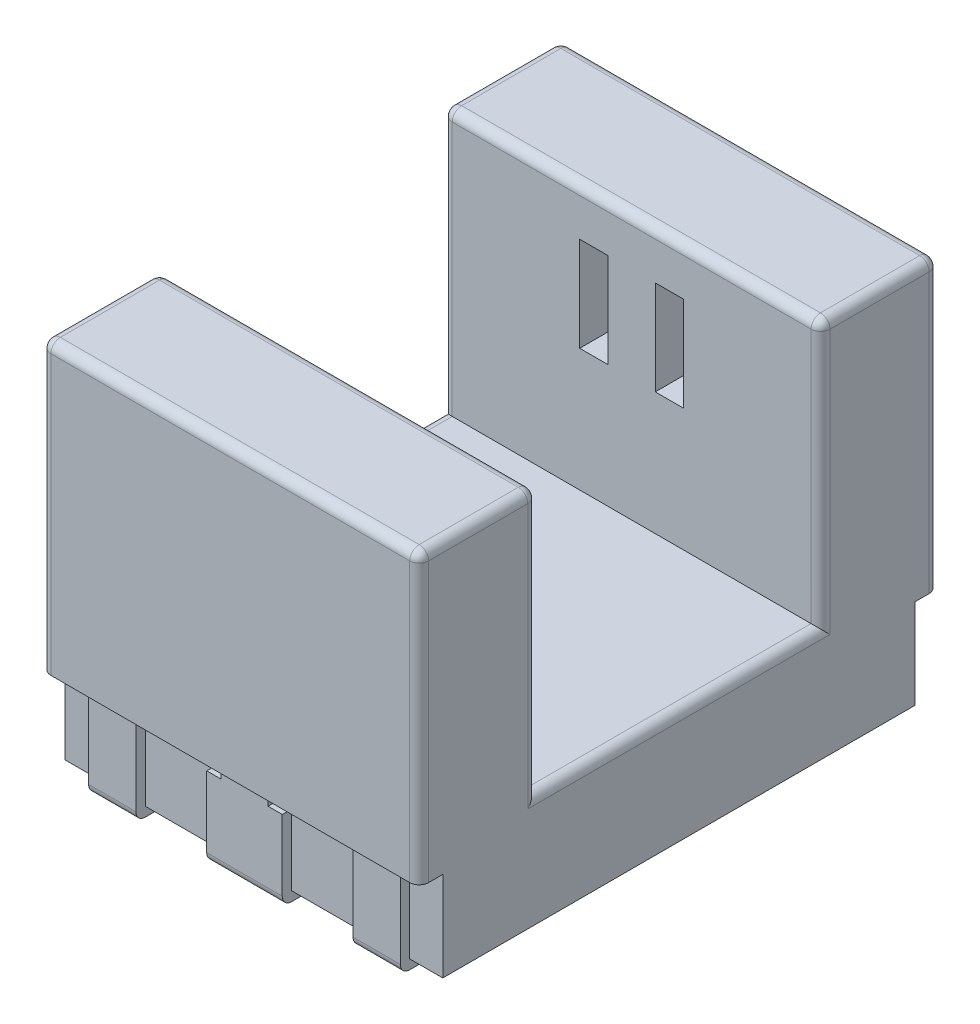
SolidWorks part; units mm, degrees
ref_plane "Plan de face" through (0, 0, 0) normal (0, 0, 1) x (1, 0, 0)
ref_plane "Plan de dessus" through (0, 0, 0) normal (0, 1, 0) x (1, 0, 0)
ref_plane "Plan de droite" through (0, 0, 0) normal (1, 0, 0) x (0, 0, -1)
sketch "Esquisse1" plane through (0, 0, 0) normal (0, 1, 0) x (1, 0, 0)
  line L0 (-2, 2.5) -> (2, -2.5) construction
  line L1 (-2, -2.5) -> (2, -2.5)
  line L2 (-2, -2.5) -> (-2, 2.5)
  line L3 (-2, 2.5) -> (2, 2.5)
  line L4 (2, -2.5) -> (2, 2.5)
  point P4 (0, 0)
  dimension "D1" = 4
  dimension "D2" = 5
extrude "Boss.-Extru.1" add sketch "Esquisse1" along normal blind 4
sketch "Esquisse3" plane through (2, 0, 0) normal (1, 0, 0) x (0, 0, -1)
  line L0 (-2.5, 4) -> (2.5, 4) construction
  line L1 (-1.5, 4) -> (1.5, 4)
  line L2 (-1.5, 4) -> (-1.5, 1.2)
  line L3 (-1.5, 1.2) -> (1.5, 1.2)
  line L4 (1.5, 4) -> (1.5, 1.2)
  line L5 (-2.5, 4) -> (-2.5, 0) construction
  dimension "D1" = 3
  dimension "D2" = 2.8
  dimension "D3" = 1
extrude "Enlèv. mat.-Extru.1" cut sketch "Esquisse3" against normal blind 4
sketch "Esquisse4" plane through (0, 0, 2.5) normal (0, 0, 1) x (1, 0, 0)
  line L0 (2, 4) -> (2, 0) construction
  line L1 (-2, 4) -> (2, 4)
  line L2 (-2, 4) -> (-2, 0.95)
  line L3 (-2, 0.95) -> (2, 0.95)
  line L4 (2, 4) -> (2, 0.95)
  line L5 (-2, 0) -> (2, 0) construction
  dimension "D1" = 0.95
extrude "Boss.-Extru.2" add sketch "Esquisse4" along normal blind 0.25
mirror "Symétrie1" about plane through (0, 0, 0) normal (0, 0, 1) of "Boss.-Extru.2"
sketch "Esquisse5" plane through (0, 0, 2.5) normal (0, 0, 1) x (1, 0, 0)
  line L0 (-2, 0) -> (2, 0) construction
  line L1 (-0.25, 0) -> (0.25, 0)
  line L2 (-0.25, 0) -> (-0.25, 0.95)
  line L3 (-0.25, 0.95) -> (0.25, 0.95)
  line L4 (0.25, 0) -> (0.25, 0.95)
  line L5 (-2, 0.95) -> (2, 0.95) construction
  line L6 (1.15, 0) -> (1.15, 0.95)
  line L7 (1.15, 0) -> (1.65, 0)
  line L8 (1.65, 0) -> (1.65, 0.95)
  line L9 (1.15, 0.95) -> (1.65, 0.95)
  line L10 (-0.25, 0) -> (-0.25, 0.95)
  line L11 (-0.25, 0) -> (0.25, 0)
  line L12 (0.25, 0) -> (0.25, 0.95)
  line L13 (-0.25, 0.95) -> (0.25, 0.95)
  line L14 (-1.65, 0) -> (-1.65, 0.95)
  line L15 (-1.65, 0) -> (-1.15, 0)
  line L16 (-1.15, 0) -> (-1.15, 0.95)
  line L17 (-1.65, 0.95) -> (-1.15, 0.95)
  line L18 (-0.25, 0) -> (1.15, 0) construction
  point P8 (0, 0)
  line M17 (2, 0.95) -> (-2, 0.95)
  line M19 (-2, 0) -> (2, 0)
  dimension "D1" = 0.5
  dimension "D4" = 1.4
  dimension "D5" = 0.95
  dimension "D6" = 1.4
  dimension "D2" = 2
  dimension "D3" = 2
extrude "Boss.-Extru.3" add sketch "Esquisse5" along normal blind 0.1 contours L16 L14 M19 M17 | L4 L2 M19 M17 | L8 L6 M19 M17
sketch "Esquisse6" plane through (0, 0, 0) normal (0, -1, 0) x (1, 0, 0)
  line L0 (-0.25, 2.6) -> (-0.25, 1.58)
  line L1 (-1.65, 2.6) -> (-1.15, 2.6)
  line L2 (-1.65, 2.6) -> (-1.65, 1.58)
  line L3 (-1.65, 1.58) -> (-1.15, 1.58)
  line L4 (-1.15, 2.6) -> (-1.15, 1.58)
  line L5 (-0.25, 2.6) -> (0.25, 2.6)
  line L6 (0.25, 2.6) -> (0.25, 1.58)
  line L7 (-0.25, 1.58) -> (0.25, 1.58)
  line L8 (1.15, 2.6) -> (1.15, 1.58)
  line L9 (1.15, 2.6) -> (1.65, 2.6)
  line L10 (1.65, 2.6) -> (1.65, 1.58)
  line L11 (1.15, 1.58) -> (1.65, 1.58)
  line L12 (-1.65, 2.6) -> (-0.25, 2.6) construction
  dimension "D1" = 0.5
  dimension "D2" = 1.02
  dimension "D4" = 1.4
  dimension "D3" = 3
extrude "Boss.-Extru.4" add sketch "Esquisse6" along normal blind 0.1
mirror "Symétrie2" about plane through (0, 0, 0) normal (0, 0, 1) of "Boss.-Extru.3", "Boss.-Extru.4"
sketch "Esquisse7" plane through (0, -0.1, 0) normal (0, -1, 0) x (1, 0, 0)
  line L0 (0.25, 2.6) -> (-0.25, 2.6) construction
  line L1 (-0.4, 1.58) -> (0.4, 1.58)
  line L2 (-0.4, 1.58) -> (-0.4, 2.6)
  line L3 (-0.4, 2.6) -> (0.4, 2.6)
  line L4 (0.4, 1.58) -> (0.4, 2.6)
  line L5 (0.25, 1.58) -> (0.25, 2.6) construction
  line L6 (-0.4, 2.6) -> (0.4, 1.58) construction
  line L7 (-0.25, 2.6) -> (-0.25, 1.58) construction
  line L8 (-0.25, 1.58) -> (0.25, 1.58) construction
  dimension "D1" = 0.8
  dimension "D2" = 0.15
extrude "Boss.-Extru.5" add sketch "Esquisse7" against normal up to surface (0.1 mm away) up to face at (0, 0, 0)
sketch "Esquisse8" plane through (0, 0, 2.6) normal (0, 0, 1) x (1, 0, 0)
  line L0 (0.4, 0) -> (0.4, -0.1) construction
  line L1 (-0.4, 0) -> (0.4, 0)
  line L2 (-0.4, 0) -> (-0.4, 0.75)
  line L3 (-0.4, 0.75) -> (0.4, 0.75)
  line L4 (0.4, 0) -> (0.4, 0.75)
  line L5 (-2, 0.95) -> (2, 0.95) construction
  dimension "D1" = 0.2
extrude "Boss.-Extru.6" add sketch "Esquisse8" against normal up to surface (0.1 mm away) up to face at (0.64, 0.38, 2.5)
sketch "Esquisse9" plane through (0, 0, 1.5) normal (0, 0, -1) x (-1, 0, 0)
  line L0 (2, 4) -> (-2, 4) construction
  line L1 (-1.25, 3.5) -> (1.25, 3.5)
  line L2 (-1.25, 3.5) -> (-1.25, 2)
  line L3 (-1.25, 2) -> (1.25, 2)
  line L4 (1.25, 3.5) -> (1.25, 2)
  line L5 (0, 4) -> (0, 1.2) construction
  line L6 (2, 1.2) -> (-2, 1.2) construction
  point P12 (0, 3.5)
  dimension "D1" = 1.5
  dimension "D2" = 2.5
  dimension "D3" = 0.5
extrude "Enlèv. mat.-Extru.2" cut sketch "Esquisse9" against normal blind 0.7 contours L2 L1 L4 L3
sketch "Esquisse10" plane through (0, 0, -1.5) normal (0, 0, 1) x (1, 0, 0)
  line L0 (0.25, 3.5) -> (0.55, 2.5) construction
  line L1 (0.25, 3.5) -> (0.55, 3.5)
  line L2 (0.25, 3.5) -> (0.25, 2.5)
  line L3 (0.25, 2.5) -> (0.55, 2.5)
  line L4 (0.55, 3.5) -> (0.55, 2.5)
  line L5 (-2, 4) -> (2, 4) construction
  line L6 (0, 4) -> (0, 1.2) construction
  line L7 (-2, 1.2) -> (2, 1.2) construction
  line L8 (-0.25, 2.5) -> (-0.55, 2.5)
  line L9 (-0.55, 3.5) -> (-0.55, 2.5)
  line L10 (-0.25, 3.5) -> (-0.55, 3.5)
  line L11 (-0.25, 3.5) -> (-0.25, 2.5)
  point P4 (0.4, 3)
  dimension "D1" = 0.3
  dimension "D2" = 1
  dimension "D3" = 0.4
  dimension "D4" = 1
extrude "Enlèv. mat.-Extru.3" cut sketch "Esquisse10" against normal blind 0.3
sketch "Esquisse11" plane through (0, 0, 0) normal (0, -1, 0) x (1, 0, 0)
  line L0 (0.5, -0.6) -> (0.9, -1)
  line L1 (0.2, 0) -> (-0.2, 0)
  line L2 (0.2, 1) -> (0.2, -1)
  line L3 (0.2, -1) -> (-0.2, -1)
  line L4 (-0.2, 1) -> (-0.2, -1)
  line L5 (0.9, -1) -> (0.5, -1)
  line L6 (0.5, -1) -> (0.5, -0.6)
  line L7 (2, 2.5) -> (-2, -2.5) construction
  line L8 (2, 0) -> (-2, 0) construction
  line L9 (2, 2.5) -> (2, -2.5) construction
  line L10 (-2, -2.5) -> (-2, 2.5) construction
  line L11 (0, 2.5) -> (0, -2.6) construction
  line L12 (0.25, -2.6) -> (-0.25, -2.6) construction
  line L13 (0.9, 1) -> (0.5, 1)
  line L14 (0.5, 0.6) -> (0.9, 1)
  line L15 (0.5, 1) -> (0.5, 0.6)
  line L16 (0.2, 1) -> (-0.2, 1)
  line L17 (-0.9, -1) -> (-0.5, -1)
  line L18 (-0.5, -0.6) -> (-0.9, -1)
  line L19 (-0.5, -1) -> (-0.5, -0.6)
  line L20 (-0.2, 1) -> (-0.2, -1)
  line L21 (0.2, 1) -> (0.2, -1)
  line L22 (-0.5, 0.6) -> (-0.9, 1)
  line L23 (-0.5, 1) -> (-0.5, 0.6)
  line L24 (-0.9, 1) -> (-0.5, 1)
  line L25 (1, -0.2) -> (1, 0.2)
  line L26 (1, 0.2) -> (-1, 0.2)
  line L27 (-1, -0.2) -> (-1, 0.2)
  line L28 (1, -0.2) -> (-1, -0.2)
  line L29 (-0.2, -1) -> (0.2, -1)
  line L30 (0.2, -1) -> (0.2, 1)
  line L31 (-0.2, 1) -> (0.2, 1)
  line L32 (-0.2, -1) -> (-0.2, 1)
  line L33 (-1, 0.2) -> (-1, -0.2)
  line L34 (-1, -0.2) -> (1, -0.2)
  line L35 (1, 0.2) -> (1, -0.2)
  line L36 (-1, 0.2) -> (1, 0.2)
  point P11 (0, 0)
  point P49 (0, 0)
  dimension "D1" = 1
  dimension "D2" = 0
  dimension "D3" = 0
  dimension "D4" = 0.4
  dimension "D5" = 0.3
  dimension "D6" = 0.4
  dimension "D7" = 0.4
  dimension "D8" = 4
extrude "Enlèv. mat.-Extru.4" cut sketch "Esquisse11" against normal blind 0.3 contours L17 L19 L18 | L28 L4 L20 L26 L27 | L21 L26 L20 L1 | L21 L28 L20 L3 | L26 L2 L16 L4 | L24 L22 L23 | L13 L15 L14 | L6 L5 L0
fillet "Congé1" radius 0.1 18 edges at (-2, 2.475, 2.75) (2, 1.2, 0) (2, 2.475, 2.75) (2, 2.6, 1.5) (0, 4, 2.75) (2, 4, 2.125) (-2, 4, 2.125) (0, 4, 1.5) (-2, 2.6, 1.5) (-2, 1.2, 0) (-2, 4, -2.125) (-2, 2.6, -1.5) (-2, 2.475, -2.75) (2, 2.475, -2.75) (0, 4, -1.5) (0, 4, -2.75) (2, 2.6, -1.5) (2, 4, -2.125)
fillet "Congé2" radius 0.1 6 edges at (1.4, -0.1, -2.6) (0, -0.1, -2.6) (-1.4, -0.1, -2.6) (1.4, -0.1, 2.6) (0, -0.1, 2.6) (-1.4, -0.1, 2.6)
fillet "Congé3" radius 0.05 70 edges at (0.7, 0, -0.8) (-0.2, 0, 0.6) (-0.5, 0.15, -0.6) (-0.7, 0.3, -0.8) (-0.7, 0, -0.8) (-0.9, 0.15, -1) (-0.7, 0.3, -1) (-0.5, 0.15, -1) (-0.7, 0, -1) (0.6, 0, 0.2) (1, 0.15, 0.2) (0.2, 0.15, 0.2) (1, 0.15, -0.2) (0.6, 0, -0.2) (0.2, 0.15, -0.2) (0.2, 0.15, -1) (0, 0, -1) (-0.2, 0.15, -1) (-0.2, 0, -0.6) (-1, 0.15, -0.2) (-0.2, 0.15, -0.2) (-0.6, 0, -0.2) (-0.2, 0.15, 0.2) (-1, 0.15, 0.2) (-0.6, 0, 0.2) (0, 0.3, -1) (-0.2, 0.3, -0.6) (-0.6, 0.3, -0.2) (-1, 0.3, 0) (-0.6, 0.3, 0.2) (-0.2, 0.3, 0.6) (0.2, 0.3, 0.6) (0.6, 0.3, 0.2) (1, 0.3, 0) (0.6, 0.3, -0.2) (0.2, 0.3, -0.6) (-0.5, 0.3, 0.8) (-0.5, 0, 0.8) (-0.7, 0.3, 0.8) (-0.5, 0.15, 0.6) (-0.7, 0, 0.8) (-0.5, 0.15, 1) (-0.7, 0.3, 1) (-0.9, 0.15, 1) (-0.7, 0, 1) (0.5, 0.3, 0.8) (0.5, 0, 0.8) (0.7, 0.3, 1) (0.5, 0.15, 1) (0.7, 0, 1) (0.5, 0.15, 0.6) (0.7, 0.3, 0.8) (0.9, 0.15, 1) (0.7, 0, 0.8) (0.7, 0.3, -1) (0.9, 0.15, -1) (0.7, 0, -1) (0.5, 0.15, -0.6) (0.5, 0.3, -0.8) (0.5, 0.15, -1) (0.5, 0, -0.8) (0.2, 0.15, 1) (0, 0.3, 1) (-0.2, 0.15, 1) (0, 0, 1) (0.2, 0, 0.6) (1, 0, 0) (0.2, 0, -0.6) (-1, 0, 0) (-0.5, 0, -0.8)
